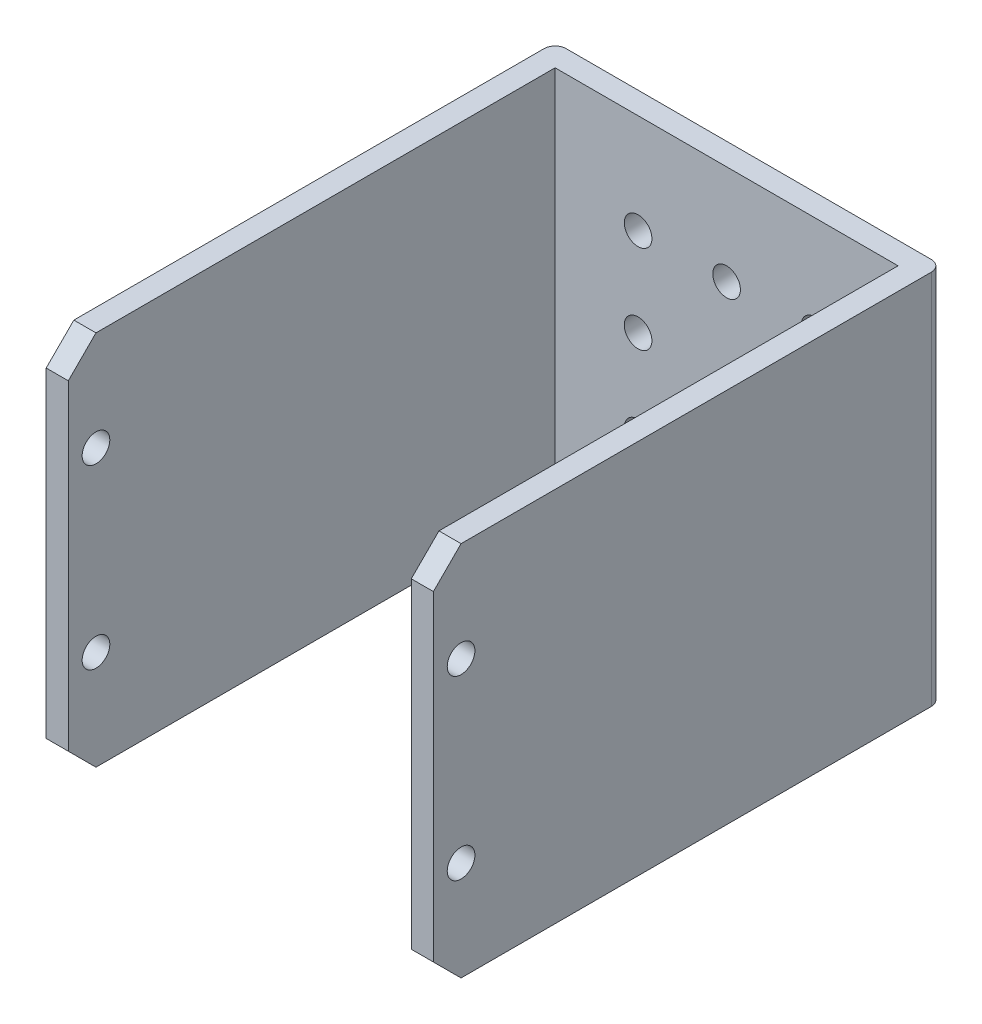
SolidWorks part; units mm, degrees
ref_plane "Front Plane" through (0, 0, 0) normal (0, 0, 1) x (1, 0, 0)
ref_plane "Top Plane" through (0, 0, 0) normal (0, 1, 0) x (1, 0, 0)
ref_plane "Right Plane" through (0, 0, 0) normal (1, 0, 0) x (0, 0, -1)
sketch "Sketch1" plane through (0, 0, 0) normal (0, 0, 1) x (1, 0, 0)
  line L1 (35, 0) -> (0, 0)
  line L2 (35, 0) -> (35, 34)
  line L3 (35, 34) -> (0, 34)
  line L4 (0, 0) -> (0, 34)
  point P6 (17.5, 0)
  dimension "D1" = 35
  dimension "D2" = 34
  dimension "D3" = 0
  dimension "D4" = 0
extrude "Boss-Extrude1" add sketch "Sketch1" along normal blind 46
sketch "Sketch3" plane through (0, 0, 46) normal (0, 0, 1) x (1, 0, 0)
  line L0 (35, 34) -> (0, 34) construction
  line L1 (2, 34) -> (33, 34)
  line L2 (2, 34) -> (2, 0)
  line L3 (2, 0) -> (33, 0)
  line L4 (33, 34) -> (33, 0)
  line L5 (0, 34) -> (0, 0) construction
  line L6 (35, 0) -> (35, 34) construction
  point P6 (2, 17)
  point P11 (33, 17)
  dimension "D1" = 2
  dimension "D2" = 34
  dimension "D3" = 2
extrude "Cut-Extrude1" cut sketch "Sketch3" against normal blind 44
fillet "Fillet1" radius 1 2 edges at (35, 17, 0) (0, 17, 0)
chamfer "Chamfer1" distance 2.5 4 edges at (34, 0, 46) (1, 0, 46) (34, 34, 46) (1, 34, 46)
sketch "Sketch4" plane through (0, 0, 0) normal (-1, 0, 0) x (0, 0, 1)
  line L0 (43.5, 34) -> (1, 34) construction
  line L1 (46, 31.5) -> (46, 2.5) construction
  circle A0 centre (43.5, 25) radius 1.25
  circle A1 centre (43.5, 9) radius 1.25
  dimension "D1" = 2.5
  dimension "D2" = 9
  dimension "D3" = 2.5
  dimension "D5" = 16
  dimension "D4" = 2
extrude "Cut-Extrude2" cut sketch "Sketch4" against normal blind 40.5
sketch "Sketch7" plane through (0, 0, 2) normal (0, 0, 1) x (1, 0, 0)
  line L1 (1, 0) -> (34, 0) construction
  line L3 (2, 34) -> (2, 0) construction
  circle A8 centre (9.5, 9) radius 1.25
  circle A9 centre (17.5, 9) radius 1.25
  circle A10 centre (25.5, 9) radius 1.25
  circle A11 centre (17.5, 17) radius 1.25 [skipped]
  circle A12 centre (25.5, 17) radius 1.25
  circle A13 centre (17.5, 25) radius 1.25
  circle A14 centre (25.5, 25) radius 1.25
  circle A15 centre (9.5, 17) radius 1.25
  circle A16 centre (9.5, 25) radius 1.25
  dimension "D2" = 2.5
  dimension "D7" = 8
  dimension "D4" = 3
  dimension "D5" = 3
  dimension "D3" = 7.5
  dimension "D6" = 8
  dimension "D17" = 9
extrude "Cut-Extrude3" cut sketch "Sketch7" against normal blind 5
